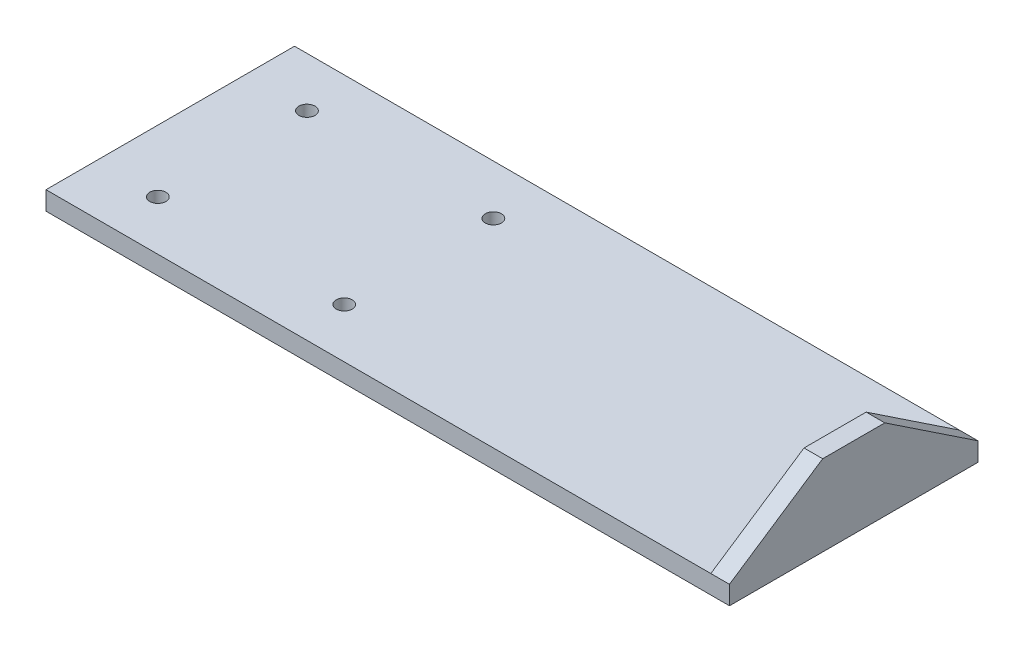
SolidWorks part; units mm, degrees
ref_plane "Front Plane" through (0, 0, 0) normal (0, 0, 1) x (1, 0, 0)
ref_plane "Top Plane" through (0, 0, 0) normal (0, 1, 0) x (1, 0, 0)
ref_plane "Right Plane" through (0, 0, 0) normal (1, 0, 0) x (0, 0, -1)
sketch "Sketch1" plane through (0, 0, 0) normal (0, 1, 0) x (1, 0, 0)
  line L1 (0, 100) -> (550, 100)
  line L2 (0, 100) -> (0, -100)
  line L3 (0, -100) -> (550, -100)
  line L4 (550, 100) -> (550, -100)
  dimension "D1" = 550
  dimension "D2" = 200
  dimension "D3" = 100
extrude "Extrude1" add sketch "Sketch1" against normal blind 15
sketch "Sketch3" plane through (0, 0, 0) normal (0, 1, 0) x (-1, 0, 0)
  line L0 (0, 100) -> (-550, 100) construction
  line L1 (-550, -100) -> (-535, -100)
  line L2 (-550, -100) -> (-550, 100)
  line L3 (-550, 100) -> (-535, 100)
  line L4 (-535, -100) -> (-535, 100)
  dimension "D1" = 15
extrude "Extrude2" add sketch "Sketch3" along normal blind 50
sketch "Sketch4" plane through (535, 0, 0) normal (-1, 0, 0) x (0, 0, 1)
  line L0 (100, 0) -> (25, 50)
  line L1 (-100, 50) -> (100, 50) construction
  line L2 (-100, 0) -> (-25, 50)
  dimension "D1" = 75
  dimension "D2" = 75
extrude "Cut-Extrude3" cut sketch "Sketch4" against normal through all and the other way through all contours L2
sketch "Sketch7" plane through (535, 0, 0) normal (-1, 0, 0) x (0, 0, 1)
  line L0 (100, 0) -> (25, 50)
  line L1 (-25, 50) -> (100, 50) construction
  dimension "D1" = 75
extrude "Cut-Extrude4" cut sketch "Sketch7" against normal through all and the other way through all flip side to cut
ref_plane "Plane2" through (250, 0, 0) normal (-1, 0, 0) x (0, 0, 1)
split line "Split Line1"
sketch "Sketch8" plane through (0, 0, 0) normal (0, 1, 0) x (-1, 0, 0)
  line L0 (0, -100) -> (0, 100) construction
  circle A0 centre (-50, -60) radius 6.5
  circle A1 centre (-200, -60) radius 6.5
  circle A2 centre (-50, 60) radius 6.5
  circle A3 centre (-200, 60) radius 6.5
  dimension "D9" = 13
  dimension "D10" = 13
  dimension "D11" = 13
  dimension "D12" = 13
  dimension "D1" = 50
  dimension "D2" = 50
  dimension "D3" = 200
  dimension "D4" = 200
  dimension "D5" = 60
  dimension "D6" = 60
  dimension "D7" = 60
  dimension "D8" = 60
extrude "Cut-Extrude5" cut sketch "Sketch8" against normal through all
